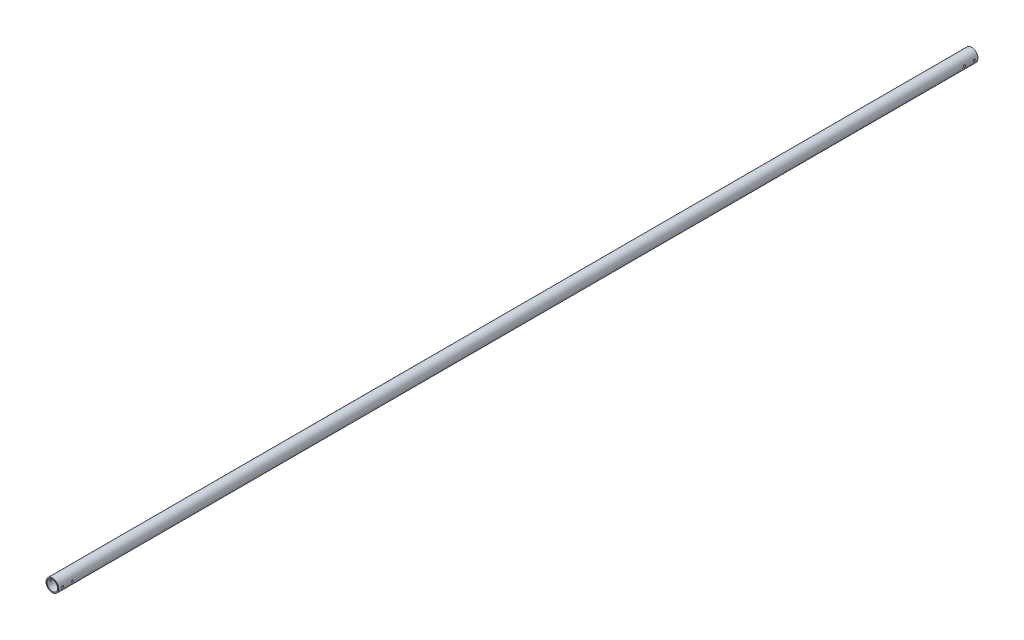
SolidWorks part; units mm, degrees
material "6061 Alloy"
ref_plane "Front Plane" through (0, 0, 0) normal (0, 0, 1) x (1, 0, 0)
ref_plane "Top Plane" through (0, 0, 0) normal (0, 1, 0) x (1, 0, 0)
ref_plane "Right Plane" through (0, 0, 0) normal (1, 0, 0) x (0, 0, -1)
sketch "Sketch1" plane through (0, 0, 0) normal (0, 0, 1) x (1, 0, 0)
  circle A0 centre (0, 0) radius 21.082
  circle A1 centre (0, 0) radius 17.526
  dimension "D1" = 42.164
  dimension "D2" = 3.556
extrude "Boss-Extrude1" add sketch "Sketch1" along normal mid plane 3035.3
ref_plane "Plane1" through (21.082, 0, 0) normal (1, 0, 0) x (0, 0, -1)
sketch "Sketch2" plane through (21.082, 0, 0) normal (1, 0, 0) x (0, 0, -1)
  line L0 (-1517.65, 21.082) -> (-1517.65, -21.082) construction
  line L1 (-1517.65, 21.082) -> (-1517.65, -21.082)
  line L2 (0, 21.082) -> (0, -21.082) construction
  line L3 (1517.65, 21.082) -> (-1517.65, 21.082) construction
  line L4 (-1517.65, -21.082) -> (1517.65, -21.082) construction
  point P0 (-1504.95, 0)
  point P3 (-1517.65, 0)
  point P4 (-1473.2, 0)
  point P12 (1473.2, 0)
  point P13 (1504.95, 0)
  dimension "D1" = 1473.2
  dimension "D2" = 31.75
hole_wizard "1/4 Clearance Hole1" positions "Sketch4" profile "Sketch5" hole size "1/4" standard "ANSI Inch" end condition through all
sketch "Sketch4" plane through (21.082, 0, 0) normal (1, 0, 0) x (0, 0, -1)
  point P0 (-1504.95, 0)
  point P4 (-1473.2, 0)
  point P6 (1504.95, 0)
  point P9 (1473.2, 0)
sketch "Sketch5" plane through (21.082, 0, 1504.95) normal (0, 1, 0) x (0, 0, -1)
  line L0 (0, 0) -> (0, 42.164)
  line L1 (0, 42.164) -> (3.3782, 42.164)
  line L2 (3.3782, 42.164) -> (3.3782, 0)
  line L5 (3.3782, 0) -> (0, 0)
  line L11 (0, -6.35) -> (0, 107.95) construction
  dimension "Thru Hole Dia." = 6.7564
  dimension "Thru Hole Depth" = 42.164
